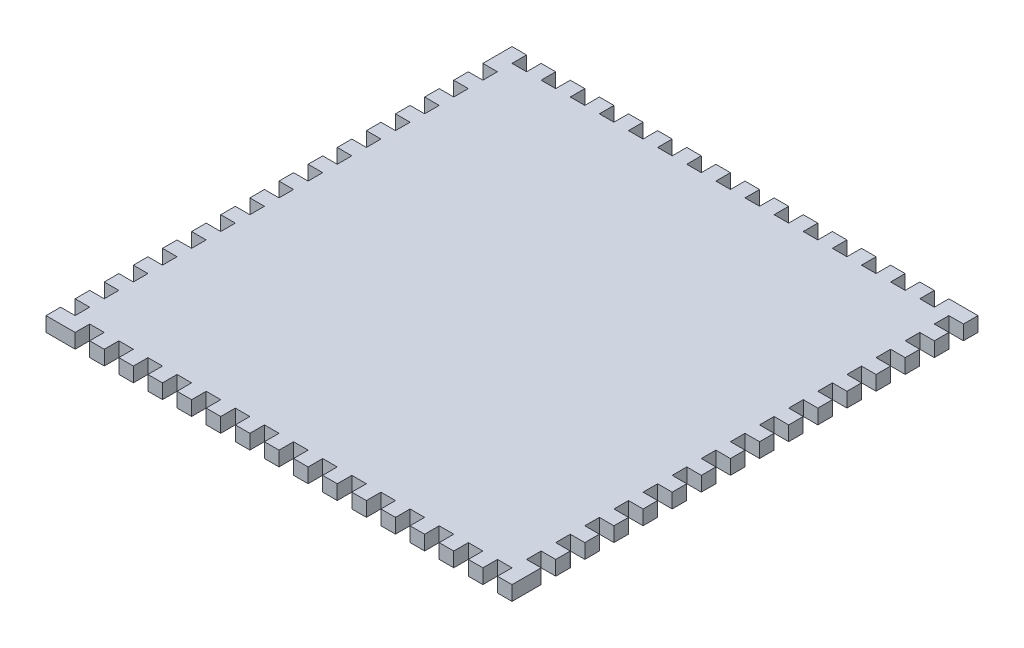
SolidWorks part; units mm, degrees
ref_plane "Front Plane" through (0, 0, 0) normal (0, 0, 1) x (1, 0, 0)
ref_plane "Top Plane" through (0, 0, 0) normal (0, 1, 0) x (1, 0, 0)
ref_plane "Right Plane" through (0, 0, 0) normal (1, 0, 0) x (0, 0, -1)
sketch "Sketch1" plane through (0, 0, 0) normal (0, 1, 0) x (1, 0, 0)
  line L1 (0, 0) -> (203.2, 0)
  line L2 (0, 0) -> (0, 203.2)
  line L3 (0, 203.2) -> (203.2, 203.2)
  line L4 (203.2, 0) -> (203.2, 203.2)
  dimension "D1" = 203.2
  dimension "D2" = 203.2
extrude "Boss-Extrude1" add sketch "Sketch1" along normal blind 6.35 contours L3 L4 L1 L2
sketch "Sketch3" plane through (0, 0, 0) normal (0, 0, 1) x (1, 0, 0)
  line L0 (0, 0) -> (203.2, 0) construction
  line L1 (203.2, 6.35) -> (196.85, 6.35)
  line L2 (203.2, 6.35) -> (203.2, 0)
  line L3 (203.2, 0) -> (196.85, 0)
  line L4 (196.85, 6.35) -> (196.85, 0)
  dimension "D1" = 6.35
extrude "Cut-Extrude1" cut sketch "Sketch3" against normal blind 6.35
pattern_linear "LPattern3" count 16 spacing 12.7 along (0, 0, -1) of "Cut-Extrude1"
sketch "Sketch5" plane through (0, 0, -203.2) normal (0, 0, -1) x (-1, 0, 0)
  line L0 (0, 6.35) -> (-203.2, 6.35) construction
  line L1 (-190.5, 6.35) -> (-184.15, 6.35)
  line L2 (-190.5, 6.35) -> (-190.5, 0)
  line L3 (-190.5, 0) -> (-184.15, 0)
  line L4 (-184.15, 6.35) -> (-184.15, 0)
  line L5 (0, 0) -> (-203.2, 0) construction
extrude "Cut-Extrude3" cut sketch "Sketch5" against normal blind 6.35
pattern_linear "LPattern4" count 15 spacing 12.7 along (-1, 0, 0) of "Cut-Extrude3"
sketch "Sketch6" plane through (0, 0, 0) normal (-1, 0, 0) x (0, 0, 1)
  line L0 (0, 6.35) -> (-203.2, 6.35) construction
  line L1 (-190.5, 6.35) -> (-184.15, 6.35)
  line L2 (-190.5, 6.35) -> (-190.5, 0)
  line L3 (-190.5, 0) -> (-184.15, 0)
  line L4 (-184.15, 6.35) -> (-184.15, 0)
  line L5 (0, 0) -> (-203.2, 0) construction
extrude "Cut-Extrude4" cut sketch "Sketch6" against normal blind 6.35
pattern_linear "LPattern5" count 15 spacing 12.7 along (0, 0, 1) of "Cut-Extrude4"
sketch "Sketch7" plane through (0, 0, 0) normal (0, 0, 1) x (1, 0, 0)
  line L0 (0, 0) -> (196.85, 0) construction
  line L1 (12.7, 0) -> (19.05, 0)
  line L2 (12.7, 0) -> (12.7, 6.35)
  line L3 (12.7, 6.35) -> (19.05, 6.35)
  line L4 (19.05, 0) -> (19.05, 6.35)
  line L5 (0, 6.35) -> (196.85, 6.35) construction
extrude "Cut-Extrude5" cut sketch "Sketch7" against normal blind 6.35
pattern_linear "LPattern6" count 15 spacing 12.7 along (1, 0, 0) of "Cut-Extrude5"
sketch "Sketch9" plane through (0, 0, -6.35) normal (0, 0, 1) x (1, 0, 0)
  line L0 (203.2, 6.35) -> (190.5, 6.35) construction
  line L1 (203.2, 0) -> (196.85, 0)
  line L2 (203.2, 0) -> (203.2, 6.35)
  line L3 (203.2, 6.35) -> (196.85, 6.35)
  line L4 (196.85, 0) -> (196.85, 6.35)
extrude "Boss-Extrude2" add sketch "Sketch9" along normal blind 6.35
